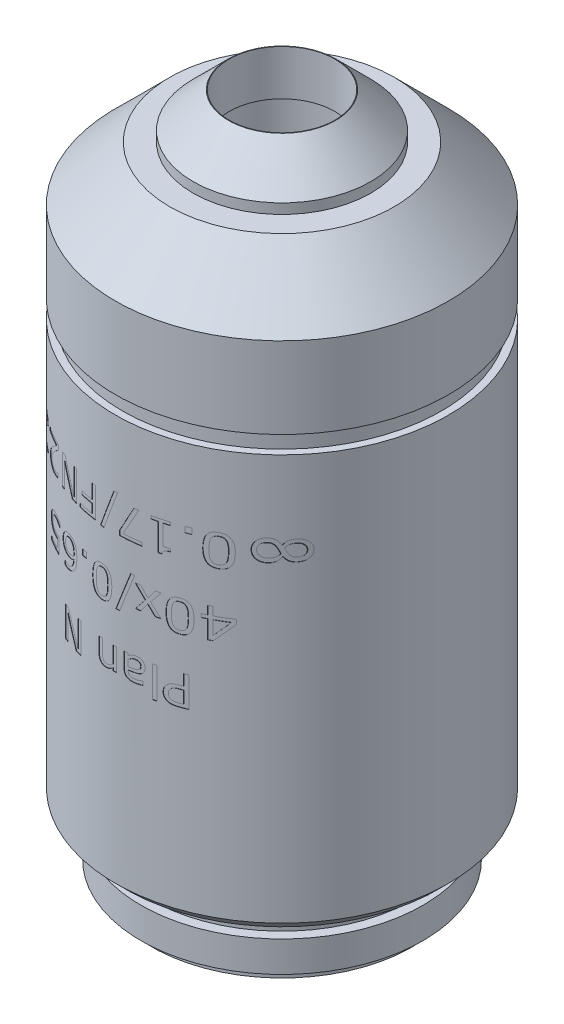
SolidWorks part; units mm, degrees
ref_plane "Front Plane" through (0, 0, 0) normal (0, 0, 1) x (1, 0, 0)
ref_plane "Top Plane" through (0, 0, 0) normal (0, 1, 0) x (1, 0, 0)
ref_plane "Right Plane" through (0, 0, 0) normal (1, 0, 0) x (0, 0, -1)
sketch "Sketch1" plane through (0, 0, 0) normal (0, 0, 1) x (1, 0, 0)
  line L0 (0, 0) -> (0, 48.768) construction
  line L1 (4.064, 45.503) -> (4.064, 6.35)
  line L2 (7.62, 0) -> (9.398, 0)
  line L3 (3.8536, 48.768) -> (3.81, 48.768)
  line L4 (0, 48.768) -> (0, 0) construction
  line L5 (10.16, 0.762) -> (10.16, 2.976)
  line L6 (10.16, 2.976) -> (9.4742, 2.976)
  line L7 (7.62, 4.5) -> (11.2395, 4.5)
  line L8 (10.16, 0.762) -> (9.398, 0.762)
  line L9 (9.398, 0.762) -> (9.398, 0)
  line L10 (12.0015, 5.262) -> (12.0015, 34.472)
  line L11 (9.4742, 4.5) -> (9.4742, 2.976)
  line L12 (12.0015, 41.584) -> (8.0825, 45.503)
  line L13 (8.0825, 45.503) -> (3.81, 45.503)
  line L14 (12.0015, 41.584) -> (4.064, 41.584)
  line L15 (8.0825, 45.503) -> (6.3958, 45.503)
  line L16 (6.3958, 45.503) -> (6.3958, 46.2259)
  line L17 (6.3958, 46.2259) -> (3.8536, 48.768)
  line L18 (11.2395, 4.5) -> (12.0015, 5.262)
  line L19 (12.0015, 5.262) -> (7.62, 5.262)
  line L20 (0, 48.768) -> (0, 0)
  line L21 (12.0015, 41.584) -> (12.0015, 35.742)
  line L22 (12.0015, 35.742) -> (12.0015, 41.584)
  line L23 (12.0015, 35.742) -> (11.4935, 35.742)
  line L24 (3.81, 48.768) -> (3.81, 45.503)
  line L25 (12.0015, 34.472) -> (11.4935, 34.472)
  line L26 (11.4935, 35.742) -> (11.4935, 34.472)
  line L27 (0, 45.503) -> (4.064, 45.503)
  line L30 (0, 0) -> (0, 6.35)
  line L31 (4.064, 6.35) -> (7.62, 6.35)
  line L32 (7.62, 0) -> (7.62, 6.35)
  point P10 (12.0015, 4.5)
  point P18 (0, 48.768)
  point P28 (3.81, 48.768)
  dimension "D1" = 12.0015
  dimension "D2" = 10.16
  dimension "D3" = 0.762
  dimension "D4" = 0.6858
  dimension "D5" = 0.762
  dimension "D6" = 1.524
  dimension "D8" = 37.084
  dimension "D9" = 0.762
  dimension "D10" = 45
  dimension "D11" = 0.508
  dimension "D12" = 1.27
  dimension "D13" = 7.62
  dimension "D14" = 6.35
revolve "Revolve1" add sketch "Sketch1" angle 360 about L0
cosmetic thread "Cosmetic Thread1" parameters "D2"=19.32
ref_plane "Plane1" through (0, 0, 25.4) normal (0, 0, 1) x (1, 0, 0)
sketch "Sketch2" plane through (0, 0, 25.4) normal (0, 0, 1) x (1, 0, 0)
  line L0 (-12.0015, 20.0527) -> (12.0015, 20.0527) construction
  line L1 (12.0015, 5.262) -> (12.0015, 34.472) construction
  line L2 (-12.0015, 34.472) -> (-12.0015, 5.262) construction
  line L3 (7.3535, 27.261) -> (7.3535, 29.727) construction
  text T0 "Plan N\r\n40x/0.65\r\n  0.17/FN22" font "Verdana" height in points 8
  text T1 "8" font "Verdana" height in points 8
extrude "Cut-Extrude7" cut sketch "Sketch2" against normal offset from surface (14.1718 mm away) 0.0254
